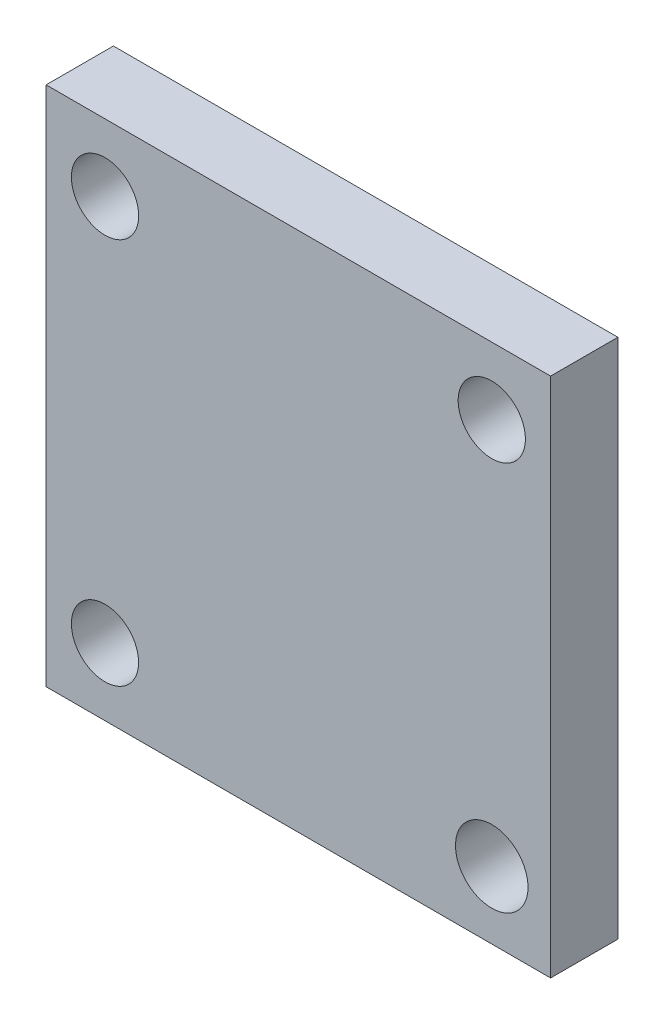
SolidWorks part; units mm, degrees
ref_plane "Front Plane" through (0, 0, 0) normal (0, 0, 1) x (1, 0, 0)
ref_plane "Top Plane" through (0, 0, 0) normal (0, 1, 0) x (1, 0, 0)
ref_plane "Right Plane" through (0, 0, 0) normal (1, 0, 0) x (0, 0, -1)
sketch "Sketch2" plane through (0, 0, 0) normal (0, 0, 1) x (1, 0, 0)
  line L0 (15.0011, -15.5011) -> (-15.0011, -15.5011)
  line L1 (15.0011, -15.5011) -> (15.0011, 15.5011)
  line L2 (15.0011, 15.5011) -> (-15.0011, 15.5011)
  line L3 (-15.0011, -15.5011) -> (-15.0011, 15.5011)
  circle A0 centre (-11.4989, 11.5033) radius 2
  circle A1 centre (11.5033, 11.5011) radius 2
  circle A2 centre (-11.5011, -11.4989) radius 2
  circle A3 centre (11.5011, -11.5011) radius 2.1563
  dimension "D1" = 4
  dimension "D2" = 4
  dimension "D3" = 4
  dimension "D4" = 4.3125
extrude "Boss-Extrude1" add sketch "Sketch2" along normal blind 4
